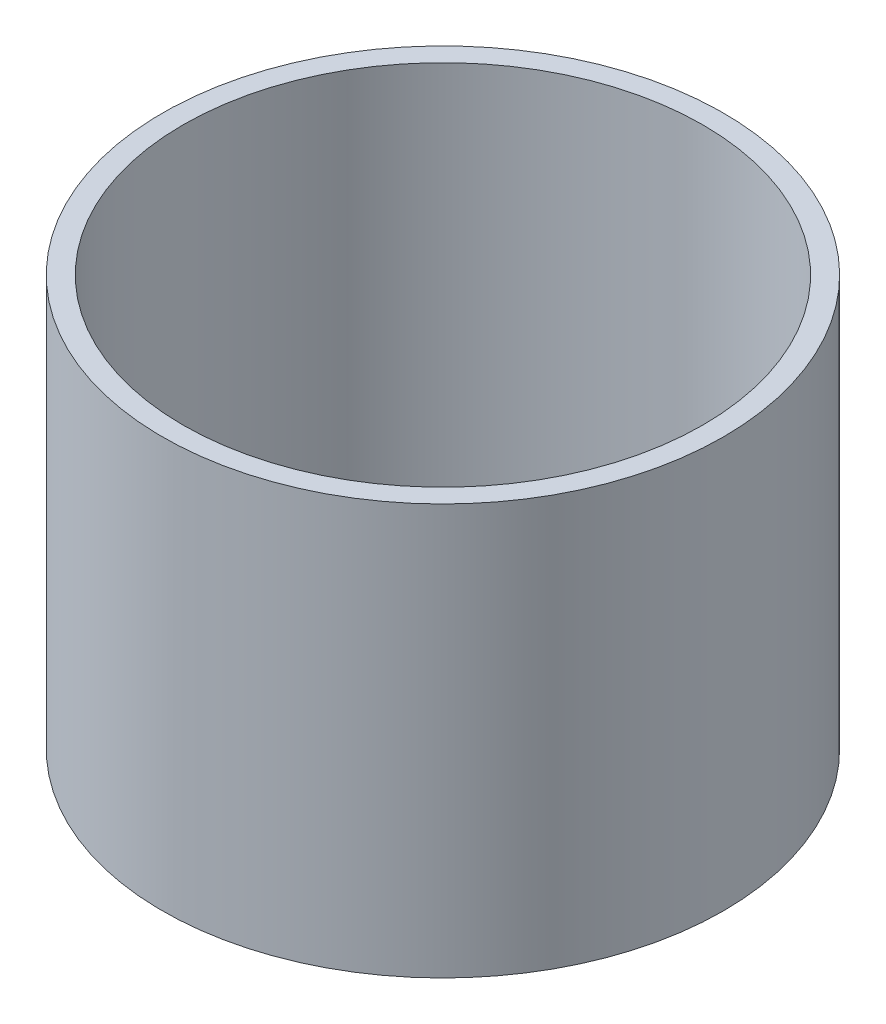
SolidWorks part; units mm, degrees
ref_plane "Front Plane" through (0, 0, 0) normal (0, 0, 1) x (1, 0, 0)
ref_plane "Top Plane" through (0, 0, 0) normal (0, 1, 0) x (1, 0, 0)
ref_plane "Right Plane" through (0, 0, 0) normal (1, 0, 0) x (0, 0, -1)
sketch "Sketch2" plane through (0, 0, 0) normal (0, 0, 1) x (1, 0, 0)
  line L0 (20.5, 30) -> (20.5, 0)
  line L1 (20.5, 0) -> (6, -5.2776)
  line L2 (6, -5.2776) -> (4.5, -5.2776)
  line L3 (4.5, -5.2776) -> (19, 0)
  line L4 (19, 0) -> (19, 30)
  line L5 (19, 30) -> (20.5, 30)
  line L6 (0, -1000) -> (0, 49000) construction
  line L7 (4.5, -5.2776) -> (10.3857, -5.2776) construction
  dimension "D1" = 1.5
  dimension "D2" = 30
  dimension "D3" = 20
  dimension "D4" = 19
  dimension "D5" = 4.5
revolve "Revolve2" add sketch "Sketch2" angle 360 about L6
